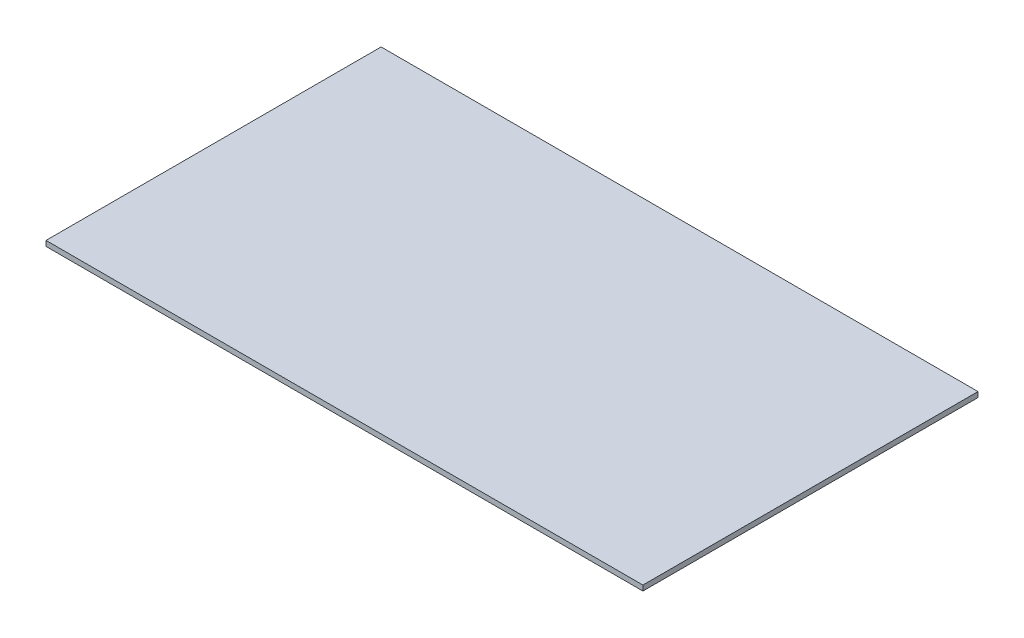
SolidWorks part; units mm, degrees
ref_plane "Front Plane" through (0, 0, 0) normal (0, 0, 1) x (1, 0, 0)
ref_plane "Top Plane" through (0, 0, 0) normal (0, 1, 0) x (1, 0, 0)
ref_plane "Right Plane" through (0, 0, 0) normal (1, 0, 0) x (0, 0, -1)
sketch "Sketch1" plane through (0, 0, 0) normal (0, 1, 0) x (1, 0, 0)
  line L1 (0, 0) -> (542.925, 0)
  line L2 (0, 0) -> (0, -304.8)
  line L3 (0, -304.8) -> (542.925, -304.8)
  line L4 (542.925, 0) -> (542.925, -304.8)
  dimension "D1" = 304.8
  dimension "D2" = 542.925
extrude "Boss-Extrude1" add sketch "Sketch1" along normal blind 4.7625 contours L1 L4 L3 L2
